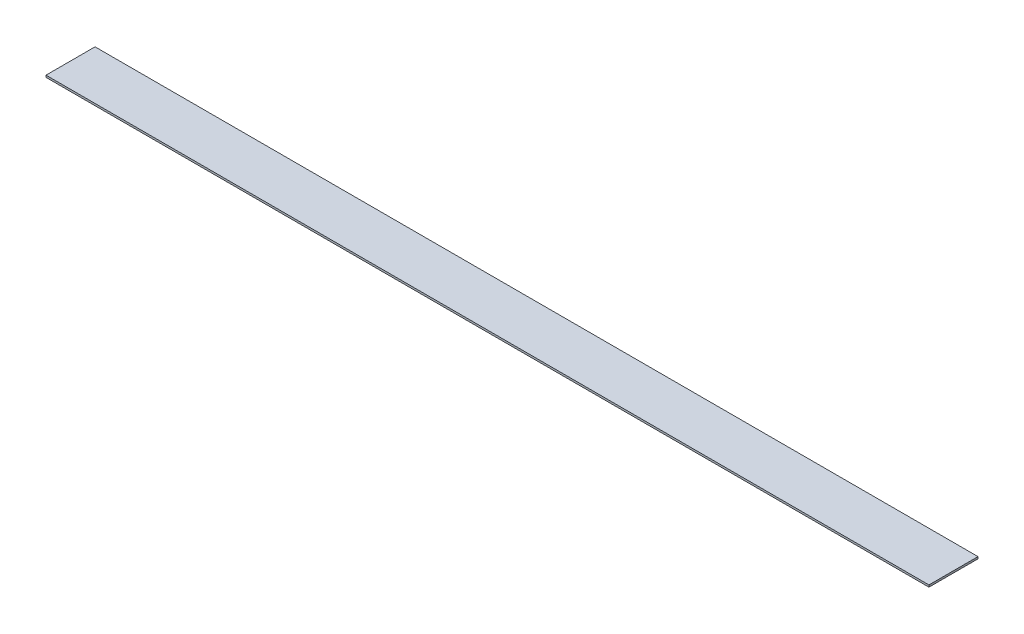
SolidWorks part; units mm, degrees
material "1023 Carbon Steel Sheet (SS)"
ref_plane "Front Plane" through (0, 0, 0) normal (0, 0, 1) x (1, 0, 0)
ref_plane "Top Plane" through (0, 0, 0) normal (0, 1, 0) x (1, 0, 0)
ref_plane "Right Plane" through (0, 0, 0) normal (1, 0, 0) x (0, 0, -1)
sketch "Sketch1" plane through (0, 0, 0) normal (0, 1, 0) x (1, 0, 0)
  line L1 (-225, 12.5) -> (225, 12.5)
  line L2 (-225, 12.5) -> (-225, -12.5)
  line L3 (-225, -12.5) -> (225, -12.5)
  line L4 (225, 12.5) -> (225, -12.5)
  line L5 (-225, 12.5) -> (225, -12.5) construction
  line L6 (-225, -12.5) -> (225, 12.5) construction
  point P0 (0, 0)
  dimension "D1" = 450
  dimension "D2" = 25
extrude "Boss-Extrude1" add sketch "Sketch1" along normal blind 1
